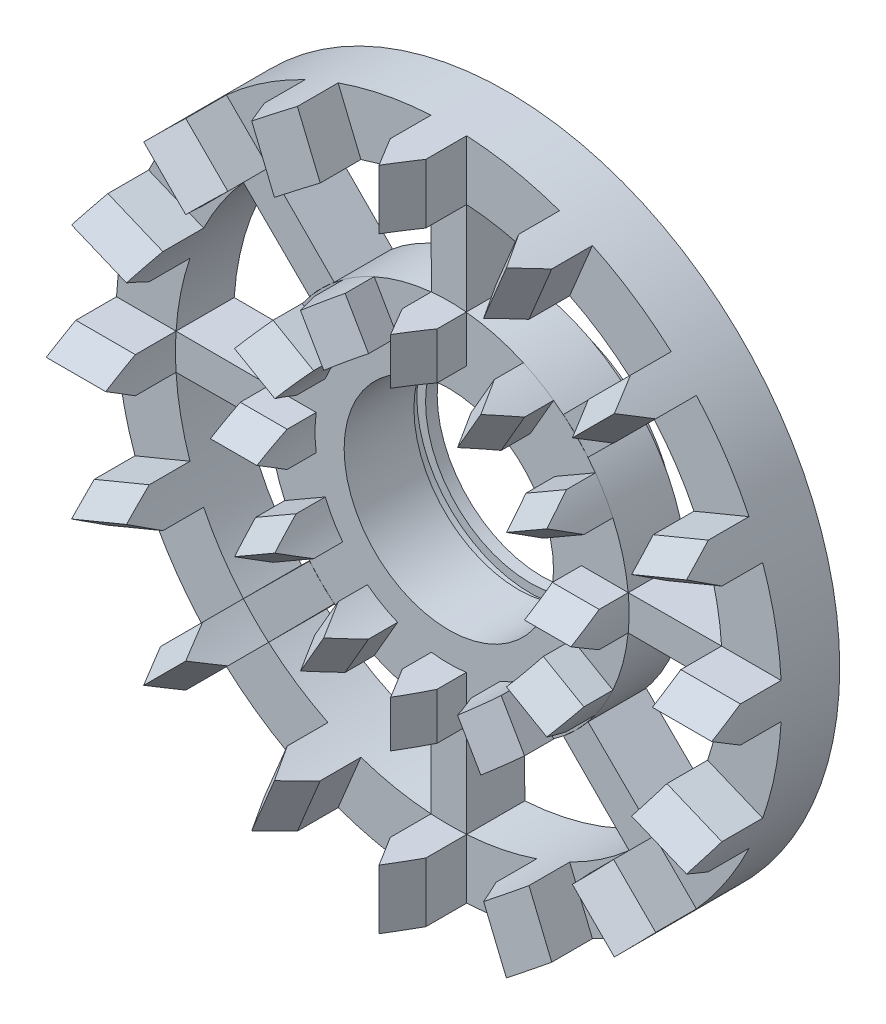
SolidWorks part; units mm, degrees
ref_plane "前视基准面" through (0, 0, 0) normal (0, 0, 1) x (1, 0, 0)
ref_plane "上视基准面" through (0, 0, 0) normal (0, 1, 0) x (1, 0, 0)
ref_plane "右视基准面" through (0, 0, 0) normal (1, 0, 0) x (0, 0, -1)
sketch "草图1" plane through (0, 0, 0) normal (0, 0, 1) x (1, 0, 0)
  line L98 (-1.5326, 28.5676) -> (-1.5326, 23.45)
  line L99 (1.5326, 23.45) -> (1.5326, 28.5676)
  arc A0 (1.5326, 23.45) -> (-1.5326, 23.45) centre (0, 0) ccw
  arc A101 (1.5326, 28.5676) -> (-1.5326, 28.5676) centre (0, 0) ccw
extrude "凸台-拉伸1" add sketch "草图1" along normal blind 6 contours L99 A101 L98 A0
sketch "草图4" plane through (0, 0, 0) normal (0, 0, 1) x (1, 0, 0)
  circle A0 centre (0, 0) radius 28.6087
  circle A1 centre (0, 0) radius 23.5
extrude "凸台-拉伸2" add sketch "草图4" against normal blind 5
ref_plane "基准面1" through (0, 23, 0) normal (0, 1, 0) x (1, 0, 0)
sketch "草图5" plane through (0, 23, 0) normal (0, 1, 0) x (1, 0, 0)
  line L0 (-1.5326, -3.5) -> (-1.5326, -6)
  line L1 (-1.5326, -6) -> (1.5326, -6)
  line L2 (1.5326, -6) -> (1.5326, -3.5)
  line L3 (1.5326, -3.5) -> (0, -6)
  line L4 (0, -6) -> (-1.5326, -3.5)
extrude "切除-拉伸1" cut sketch "草图5" along normal blind 6 contours L1 L4 L0 | L2 L3 L1
pattern_circular "阵列(圆周)1" count 16 every 22.5 about axis through (0, 0, 0) along (0, 0, 1) of "凸台-拉伸1", "切除-拉伸1"
sketch "草图6" plane through (0, 0, 0) normal (0, 0, 1) x (1, 0, 0)
  line L93 (1.5, 11.4018) -> (1.5, 15.4272)
  line L94 (-1.5, 15.4272) -> (-1.5, 11.4018)
  arc A0 (1.5, 11.4018) -> (-1.5, 11.4018) centre (0, 0) ccw
  arc A95 (1.5, 15.4272) -> (-1.5, 15.4272) centre (0, 0) ccw
extrude "凸台-拉伸3" add sketch "草图6" along normal blind 5 separate body contours L93 A95 L94 A0
ref_plane "基准面2" through (0, 11, 0) normal (0, 1, 0) x (1, 0, 0)
sketch "草图7" plane through (0, 11, 0) normal (0, 1, 0) x (1, 0, 0)
  line L0 (-1.5, -5) -> (1.5, -5)
  line L1 (1.5, -5) -> (1.5, -2.5)
  line L2 (1.5, -2.5) -> (0, -5)
  line L3 (0, -5) -> (-1.5, -2.5)
  line L4 (-1.5, -2.5) -> (-1.5, -5)
extrude "切除-拉伸2" cut sketch "草图7" along normal blind 5 contours L3 L4 L0 | L1 L2 L0
sketch "草图8" plane through (0, 0, 0) normal (0, 0, 1) x (1, 0, 0)
  circle A0 centre (0, 0) radius 15.4894
  circle A1 centre (0, 0) radius 11.5
pattern_circular "阵列(圆周)7" count 12 over 360 about axis through (0, 0, 0) along (0, 0, 1) of bodies 116
extrude "凸台-拉伸4" add sketch "草图8" against normal blind 5
sketch "草图9" plane through (0, 0, 0) normal (0, 0, 1) x (1, 0, 0)
  line L0 (-1.5326, 23.45) -> (-1.5, 15.4166)
  line L1 (1.5326, 23.45) -> (1.5, 15.4272)
  line L2 (15.4979, 17.6654) -> (9.8405, 11.9618)
  line L3 (17.6654, 15.4979) -> (11.9694, 9.8481)
  line L4 (23.45, 1.5326) -> (15.4166, 1.5)
  line L5 (23.45, -1.5326) -> (15.4272, -1.5)
  line L6 (17.6654, -15.4979) -> (11.9618, -9.8405)
  line L7 (15.4979, -17.6654) -> (9.8481, -11.9694)
  line L8 (1.5326, -23.45) -> (1.5, -15.4166)
  line L9 (-1.5326, -23.45) -> (-1.5, -15.4272)
  line L10 (-15.4979, -17.6654) -> (-9.8405, -11.9618)
  line L11 (-17.6654, -15.4979) -> (-11.9694, -9.8481)
  line L12 (-23.45, -1.5326) -> (-15.4166, -1.5)
  line L13 (-23.45, 1.5326) -> (-15.4272, 1.5)
  line L14 (-17.6654, 15.4979) -> (-11.9618, 9.8405)
  line L15 (-15.4979, 17.6654) -> (-9.8481, 11.9694)
  arc A0 (1.5326, 23.45) -> (-1.5326, 23.45) centre (0, 0) ccw
  arc A1 (1.5, 15.4272) -> (-1.5, 15.4272) centre (0, 0) ccw
  arc A2 (17.6654, 15.4979) -> (15.4979, 17.6654) centre (0, 0) ccw
  arc A3 (11.9694, 9.8481) -> (9.848, 11.9694) centre (0, 0) ccw
  arc A4 (23.45, -1.5326) -> (23.45, 1.5326) centre (0, 0) ccw
  arc A5 (15.4272, -1.5) -> (15.4272, 1.5) centre (0, 0) ccw
  arc A6 (15.4979, -17.6654) -> (17.6654, -15.4979) centre (0, 0) ccw
  arc A7 (9.8481, -11.9694) -> (11.9694, -9.848) centre (0, 0) ccw
  arc A8 (-1.5326, -23.45) -> (1.5326, -23.45) centre (0, 0) ccw
  arc A9 (-1.5, -15.4272) -> (1.5, -15.4272) centre (0, 0) ccw
  arc A10 (-17.6654, -15.4979) -> (-15.4979, -17.6654) centre (0, 0) ccw
  arc A11 (-11.9694, -9.8481) -> (-9.848, -11.9694) centre (0, 0) ccw
  arc A12 (-23.45, 1.5326) -> (-23.45, -1.5326) centre (0, 0) ccw
  arc A13 (-15.4272, 1.5) -> (-15.4272, -1.5) centre (0, 0) ccw
  arc A14 (-15.4979, 17.6654) -> (-17.6654, 15.4979) centre (0, 0) ccw
  arc A15 (-9.8481, 11.9694) -> (-11.9694, 9.848) centre (0, 0) ccw
  point P43 (0, 0)
extrude "凸台-拉伸5" add sketch "草图9" against normal blind 5 contours A1 L1 A0 L0 | A3 L3 A2 L2 | A5 L5 A4 L4 | A7 L7 A6 L6 | A9 L9 A8 L8 | A11 L11 A10 L10 | A13 L13 A12 L12 | A15 L15 A14 L14
sketch "草图10" plane through (0, 0, 0) normal (0, 0, 1) x (1, 0, 0)
  circle A0 centre (0, 0) radius 11.5
  circle A1 centre (0, 0) radius 9
extrude "凸台-拉伸6" add sketch "草图10" against normal blind 8
sketch "草图11" plane through (0, 0, 0) normal (1, 0, 0) x (0, 0, -1)
  line L0 (8, 0) -> (0, 0) construction
  line L1 (6, 9) -> (7, 9)
  line L5 (6, 9) -> (6, 9.75)
  line L6 (6, 9.75) -> (7, 9.75)
  line L7 (7, 9.75) -> (7, 9)
revolve "切除-旋转1" cut sketch "草图11" angle 360 about L0
